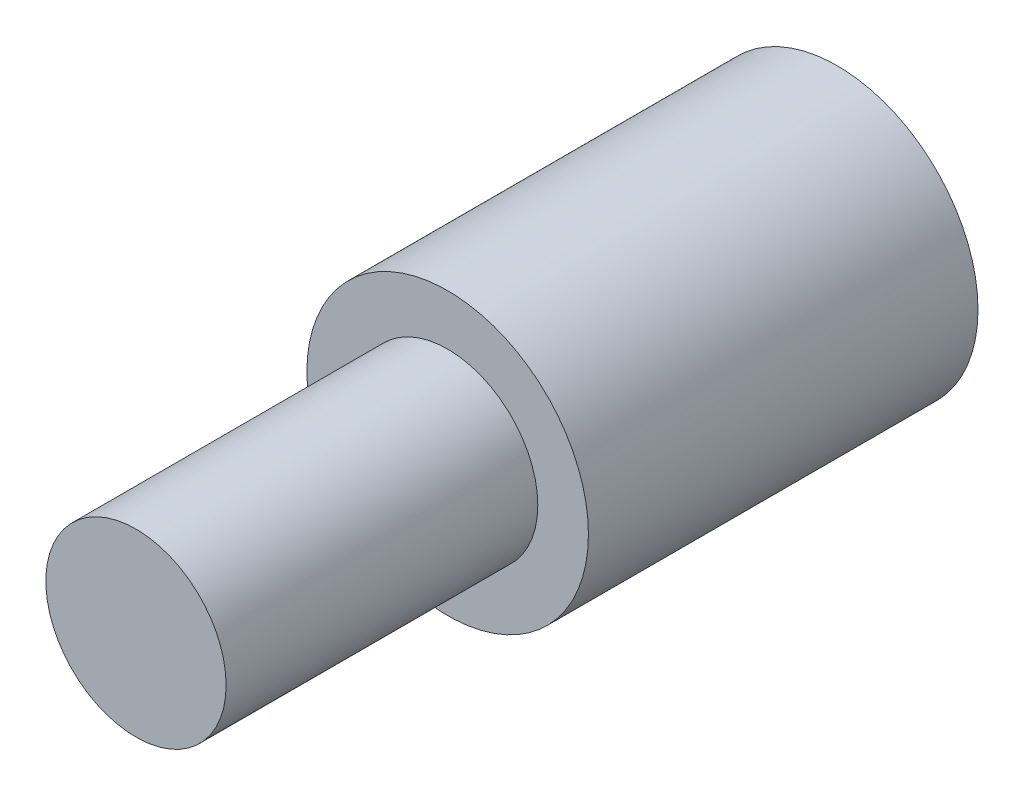
SolidWorks part; units mm, degrees
ref_plane "Front Plane" through (0, 0, 0) normal (0, 0, 1) x (1, 0, 0)
ref_plane "Top Plane" through (0, 0, 0) normal (0, 1, 0) x (1, 0, 0)
ref_plane "Right Plane" through (0, 0, 0) normal (1, 0, 0) x (0, 0, -1)
sketch "Sketch1" plane through (0, 0, 0) normal (0, 0, 1) x (1, 0, 0)
  circle A0 centre (-23.3473, 22.5825) radius 21.68
  circle A1 centre (-23.3473, 22.5825) radius 13.8828
sketch "Sketch2" plane through (0, 0, 0) normal (0, 0, 1) x (1, 0, 0)
  circle A0 centre (-23.3473, 22.5825) radius 21.68
extrude "Boss-Extrude1" add sketch "Sketch2" along normal blind 60
sketch "Sketch4" plane through (0, 0, 0) normal (0, 0, 1) x (1, 0, 0)
  circle A0 centre (-23.3473, 22.5825) radius 13.8828
extrude "Boss-Extrude2" add sketch "Sketch4" along normal blind 108
